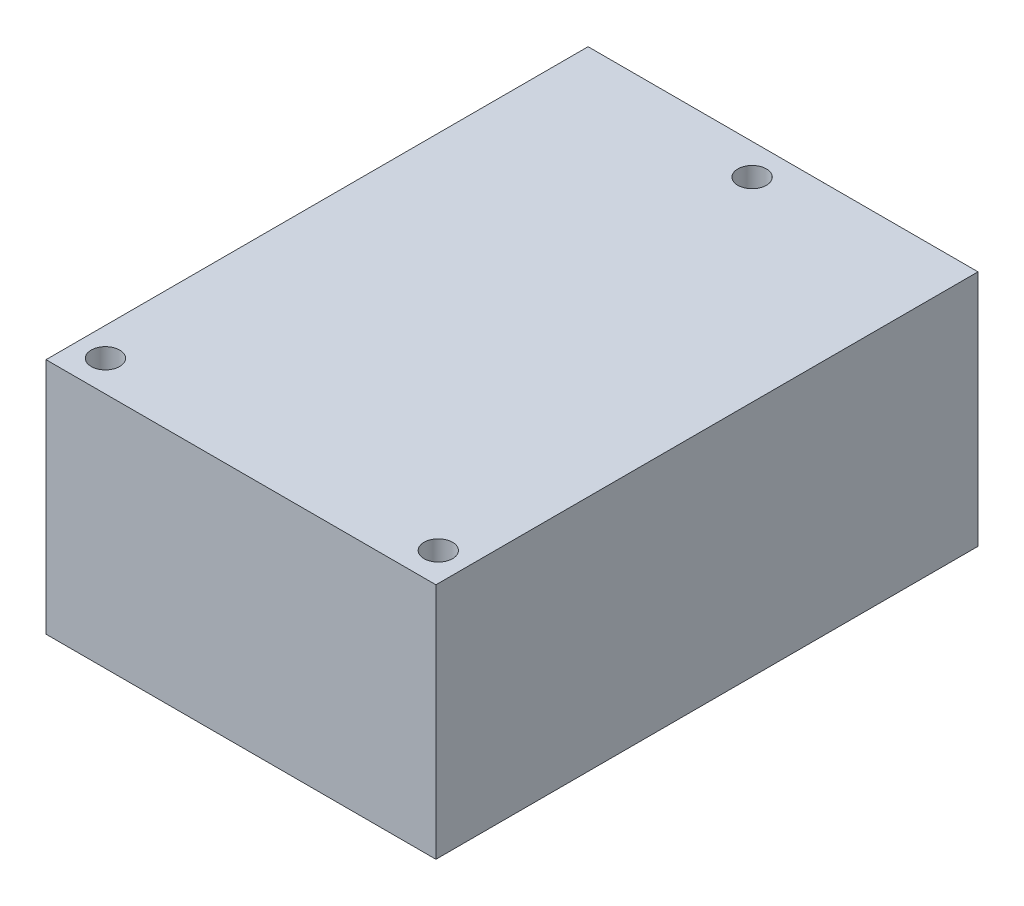
SolidWorks part; units mm, degrees
ref_plane "前视基准面" through (0, 0, 0) normal (0, 0, 1) x (1, 0, 0)
ref_plane "上视基准面" through (0, 0, 0) normal (0, 1, 0) x (1, 0, 0)
ref_plane "右视基准面" through (0, 0, 0) normal (1, 0, 0) x (0, 0, -1)
other "质心 (COM)"
sketch "草图1" plane through (0, 0, 0) normal (0, 1, 0) x (1, 0, 0)
  line L1 (-20.5, 28.5) -> (20.5, 28.5)
  line L2 (-20.5, 28.5) -> (-20.5, -28.5)
  line L3 (-20.5, -28.5) -> (20.5, -28.5)
  line L4 (20.5, 28.5) -> (20.5, -28.5)
  line L5 (-20.5, 28.5) -> (20.5, -28.5) construction
  line L6 (-20.5, -28.5) -> (20.5, 28.5) construction
  point P0 (0, 0)
  dimension "D1" = 41
  dimension "D2" = 57
extrude "凸台-拉伸1" add sketch "草图1" along normal blind 25
sketch "草图2" plane through (0, 25, 0) normal (0, 1, 0) x (1, 0, 0)
  line L0 (0, 25.25) -> (0, -25.25) construction
  line L1 (-17.5, -25.25) -> (17.5, -25.25) construction
  circle A0 centre (0, 25.25) radius 1.5
  circle A1 centre (-17.5, -25.25) radius 1.5
  circle A2 centre (17.5, -25.25) radius 1.5
  point P4 (0, 0)
  point P8 (0, -25.25)
  dimension "D2" = 3
  dimension "D1" = 50.5
  dimension "D3" = 35
extrude "切除-拉伸1" cut sketch "草图2" against normal through all
